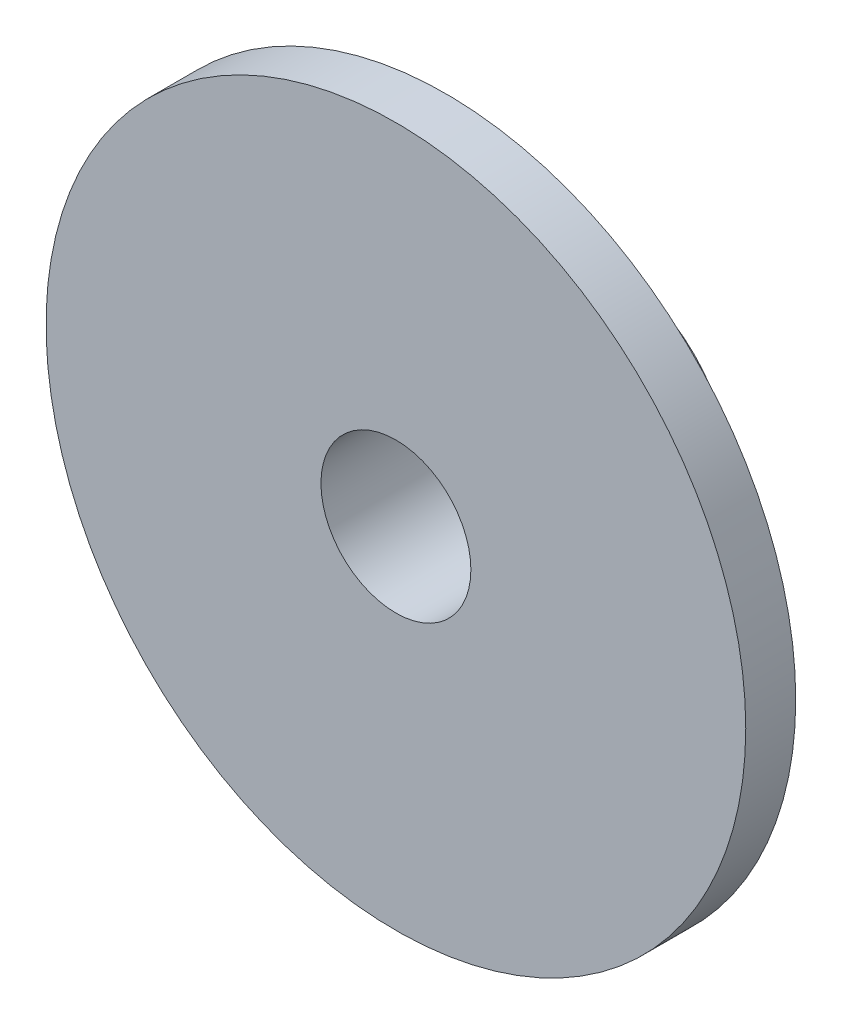
SolidWorks part; units mm, degrees
material "6061-T6 (SS)"
ref_plane "Front Plane" through (0, 0, 0) normal (0, 0, 1) x (1, 0, 0)
ref_plane "Top Plane" through (0, 0, 0) normal (0, 1, 0) x (1, 0, 0)
ref_plane "Right Plane" through (0, 0, 0) normal (1, 0, 0) x (0, 0, -1)
sketch "Sketch1" plane through (0, 0, 0) normal (0, 0, 1) x (1, 0, 0)
  circle A0 centre (0, 0) radius 4.7625
  circle A1 centre (0, 0) radius 22.225
  dimension "D1" = 9.525
  dimension "D2" = 44.45
extrude "Boss-Extrude1" add sketch "Sketch1" along normal blind 3.175
sketch "Sketch2" plane through (0, 0, 0) normal (0, 0, -1) x (-1, 0, 0)
  circle A0 centre (0, 0) radius 4.7625 construction
  circle A1 centre (0, 0) radius 4.7625
  circle A2 centre (0, 0) radius 7.9375
  dimension "D1" = 3.175
extrude "Boss-Extrude2" add sketch "Sketch2" along normal blind 10.16
